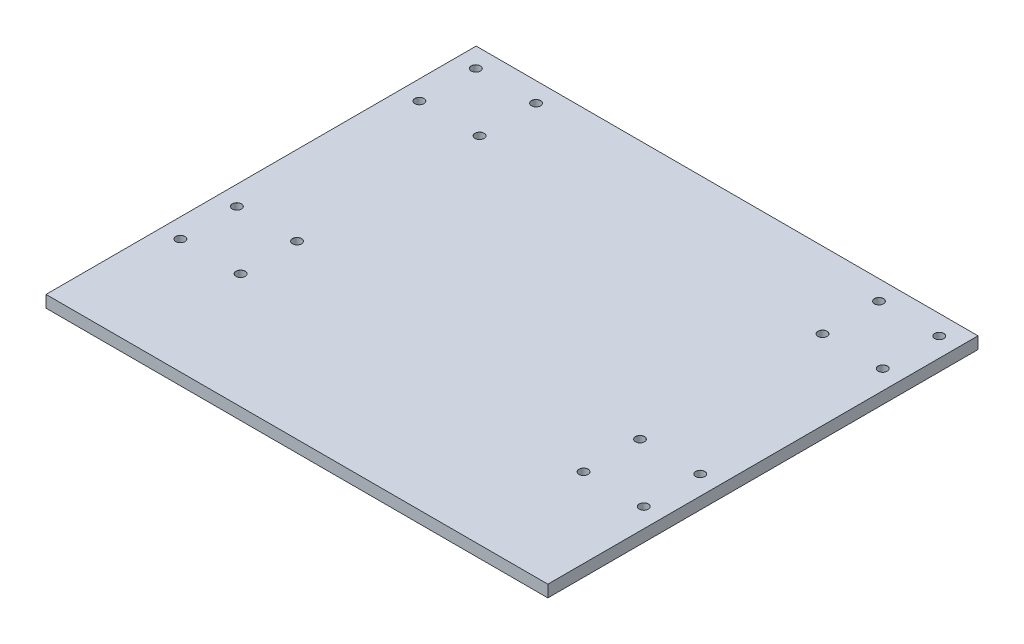
SolidWorks part; units mm, degrees
ref_plane "Front Plane" through (0, 0, 0) normal (0, 0, 1) x (1, 0, 0)
ref_plane "Top Plane" through (0, 0, 0) normal (0, 1, 0) x (1, 0, 0)
ref_plane "Right Plane" through (0, 0, 0) normal (1, 0, 0) x (0, 0, -1)
sketch "Sketch1" plane through (0, 0, 0) normal (0, 1, 0) x (1, 0, 0)
  line L1 (-133.35, 114.3) -> (133.35, 114.3)
  line L2 (-133.35, 114.3) -> (-133.35, -114.3)
  line L3 (-133.35, -114.3) -> (133.35, -114.3)
  line L4 (133.35, 114.3) -> (133.35, -114.3)
  line L5 (-133.35, 114.3) -> (133.35, -114.3) construction
  line L6 (-133.35, -114.3) -> (133.35, 114.3) construction
  point P0 (0, 0)
  dimension "D1" = 266.7
  dimension "D2" = 228.6
extrude "Boss-Extrude1" add sketch "Sketch1" along normal blind 6.35
ref_plane "Top" through (0, 0, -114.3) normal (0, 0, -1) x (-1, 0, 0)
hole_wizard "M4 Clearance Hole1" positions "Sketch2" profile "Sketch3" hole size "M4" standard "ANSI Metric" end condition up to next
sketch "Sketch2" plane through (0, 6.35, 0) normal (0, 1, 0) x (1, 0, 0)
  circle A0 centre (123.125, 103.9) radius 2.1 construction
  circle A1 centre (91.125, 103.9) radius 2.1 construction
  circle A2 centre (91.125, 73.9) radius 2.1 construction
  circle A3 centre (123.125, -53.1) radius 2.1 construction
  circle A4 centre (123.125, -23.1) radius 2.1 construction
  circle A5 centre (123.125, 73.9) radius 2.1 construction
  circle A6 centre (-123.125, 103.9) radius 2.1 construction
  circle A7 centre (-91.125, 103.9) radius 2.1 construction
  circle A8 centre (-91.125, 73.9) radius 2.1 construction
  circle A9 centre (91.125, -23.1) radius 2.1 construction
  circle A10 centre (91.125, -53.1) radius 2.1 construction
  circle A11 centre (-123.125, -53.1) radius 2.1 construction
  circle A12 centre (-91.125, -53.1) radius 2.1 construction
  circle A13 centre (-91.125, -23.1) radius 2.1 construction
  circle A14 centre (-123.125, -23.1) radius 2.1 construction
  circle A15 centre (-123.125, 73.9) radius 2.1 construction
  circle A16 centre (123.125, 103.9) radius 2.1 construction
  circle A17 centre (91.125, 103.9) radius 2.1 construction
  circle A18 centre (91.125, 73.9) radius 2.1 construction
  circle A19 centre (123.125, -53.1) radius 2.1 construction
  circle A20 centre (123.125, -23.1) radius 2.1 construction
  circle A21 centre (123.125, 73.9) radius 2.1 construction
  circle A22 centre (-123.125, 103.9) radius 2.1 construction
  circle A23 centre (-91.125, 103.9) radius 2.1 construction
  circle A24 centre (-91.125, 73.9) radius 2.1 construction
  circle A25 centre (91.125, -23.1) radius 2.1 construction
  circle A26 centre (91.125, -53.1) radius 2.1 construction
  circle A27 centre (-123.125, -53.1) radius 2.1 construction
  circle A28 centre (-91.125, -53.1) radius 2.1 construction
  circle A29 centre (-91.125, -23.1) radius 2.1 construction
  circle A30 centre (-123.125, -23.1) radius 2.1 construction
  circle A31 centre (-123.125, 73.9) radius 2.1 construction
  point P1 (123.125, 103.9)
  point P3 (91.125, 103.9)
  point P5 (91.125, 73.9)
  point P7 (123.125, -53.1)
  point P9 (123.125, -23.1)
  point P11 (123.125, 73.9)
  point P13 (-123.125, 103.9)
  point P15 (-91.125, 103.9)
  point P17 (-91.125, 73.9)
  point P21 (91.125, -53.1)
  point P23 (-123.125, -53.1)
  point P25 (-91.125, -53.1)
  point P27 (-91.125, -23.1)
  point P29 (-123.125, -23.1)
  point P31 (-123.125, 73.9)
  point P71 (91.125, -23.1)
sketch "Sketch3" plane through (123.125, 6.35, -103.9) normal (1, 0, 0) x (0, 0, 1)
  line L0 (0, 0) -> (0, 6.35)
  line L1 (0, 6.35) -> (2.4, 6.35)
  line L2 (2.4, 6.35) -> (2.4, 0.025)
  line L3 (2.4, 0.025) -> (2.425, 0)
  line L5 (2.425, 0) -> (0, 0)
  line L6 (-2.4, 0.025) -> (-2.425, 0) construction
  line L11 (0, -6.35) -> (0, 107.95) construction
  dimension "Thru Hole Dia." = 4.8
  dimension "Thru Hole Depth" = 6.35
  dimension "Near C'Sink Dia." = 4.85
  dimension "Near C'Sink Angle" = 90
